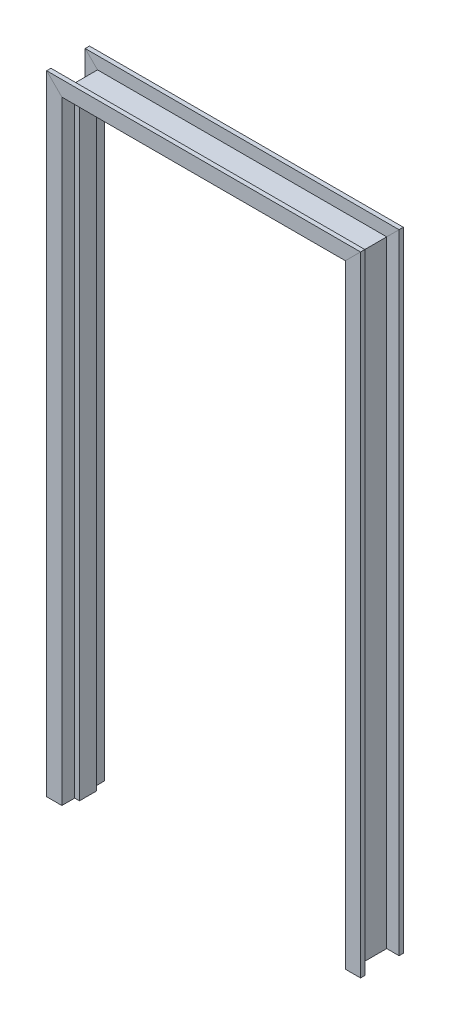
SolidWorks part; units mm, degrees
material "AISI 1020 Steel, Cold Rolled"
ref_plane "Front Plane" through (0, 0, 0) normal (0, 0, 1) x (1, 0, 0)
ref_plane "Top Plane" through (0, 0, 0) normal (0, 1, 0) x (1, 0, 0)
ref_plane "Right Plane" through (0, 0, 0) normal (1, 0, 0) x (0, 0, -1)
sketch "Sketch1" plane through (0, 0, 0) normal (0, 0, 1) x (1, 0, 0)
  line L0 (0, 0) -> (0, 2032)
  line L1 (0, 2032) -> (914.4, 2032)
  line L2 (914.4, 2032) -> (914.4, 0)
  dimension "D1" = 2032
  dimension "D2" = 914.4
  dimension "D3" = 2032
sketch "Sketch2" plane through (0, 0, 0) normal (0, 1, 0) x (1, 0, 0)
  line L0 (0, 0) -> (0, 57.15)
  line L1 (0, 57.15) -> (-15.875, 57.15)
  line L2 (-15.875, 57.15) -> (-15.875, 100.0125)
  line L3 (-15.875, 100.0125) -> (-66.675, 100.0125)
  line L4 (-66.675, 100.0125) -> (-66.675, 85.725)
  line L5 (-66.675, 85.725) -> (-25.4, 85.725)
  line L6 (-25.4, 85.725) -> (-25.4, -28.575)
  line L7 (-25.4, -28.575) -> (-66.675, -28.575)
  line L8 (-66.675, -28.575) -> (-66.675, -42.8625)
  line L9 (-66.675, -42.8625) -> (-15.875, -42.8625)
  line L10 (-15.875, -42.8625) -> (-15.875, 0)
  line L11 (-15.875, 0) -> (0, 0)
  dimension "D1" = 142.875
  dimension "D2" = 114.3
  dimension "D3" = 25.4
  dimension "D4" = 57.15
  dimension "D5" = 15.875
  dimension "D6" = 50.8
  dimension "D7" = 50.8
sweep "Sweep1" add profiles "Sketch2" path "Sketch1"
